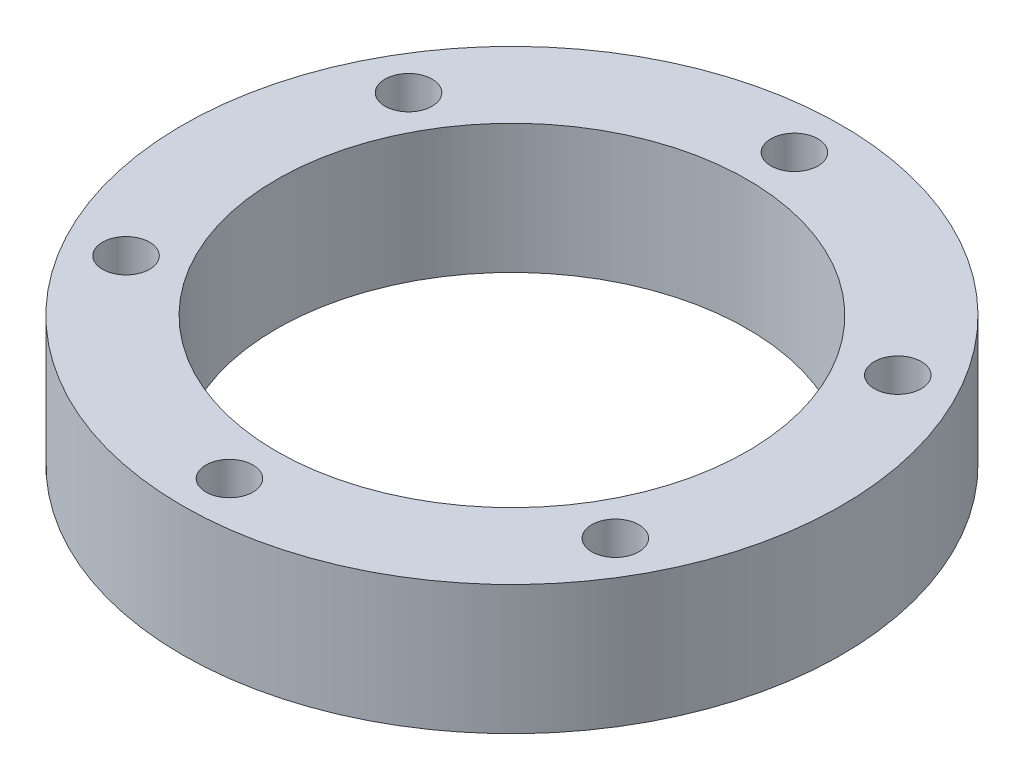
SolidWorks part; units mm, degrees
ref_plane "Front Plane" through (0, 0, 0) normal (0, 0, 1) x (1, 0, 0)
ref_plane "Top Plane" through (0, 0, 0) normal (0, 1, 0) x (1, 0, 0)
ref_plane "Right Plane" through (0, 0, 0) normal (1, 0, 0) x (0, 0, -1)
sketch "Sketch1" plane through (0, 0, 0) normal (0, 1, 0) x (1, 0, 0)
  circle A0 centre (0, 0) radius 17.5
extrude "Boss-Extrude1" add sketch "Sketch1" along normal blind 6.86
sketch "Sketch2" plane through (0, 6.86, 0) normal (0, 1, 0) x (1, 0, 0)
  circle A0 centre (0, 0) radius 12.5
  circle A1 centre (0, 0) radius 17.5 construction
  dimension "D1" = 5
extrude "Cut-Extrude1" cut sketch "Sketch2" against normal blind 6.86
sketch "Sketch3" plane through (0, 6.86, 0) normal (0, 1, 0) x (1, 0, 0)
  circle A0 centre (0, 15) radius 1.25
  circle A1 centre (0, 0) radius 17.5 construction
  dimension "D1" = 15
extrude "Cut-Extrude2" cut sketch "Sketch3" against normal blind 6.86 contours A0
pattern_circular "CirPattern2" count 6 every 60 about axis through (0, 0, 0) along (0, 1, 0) of "Cut-Extrude2"
